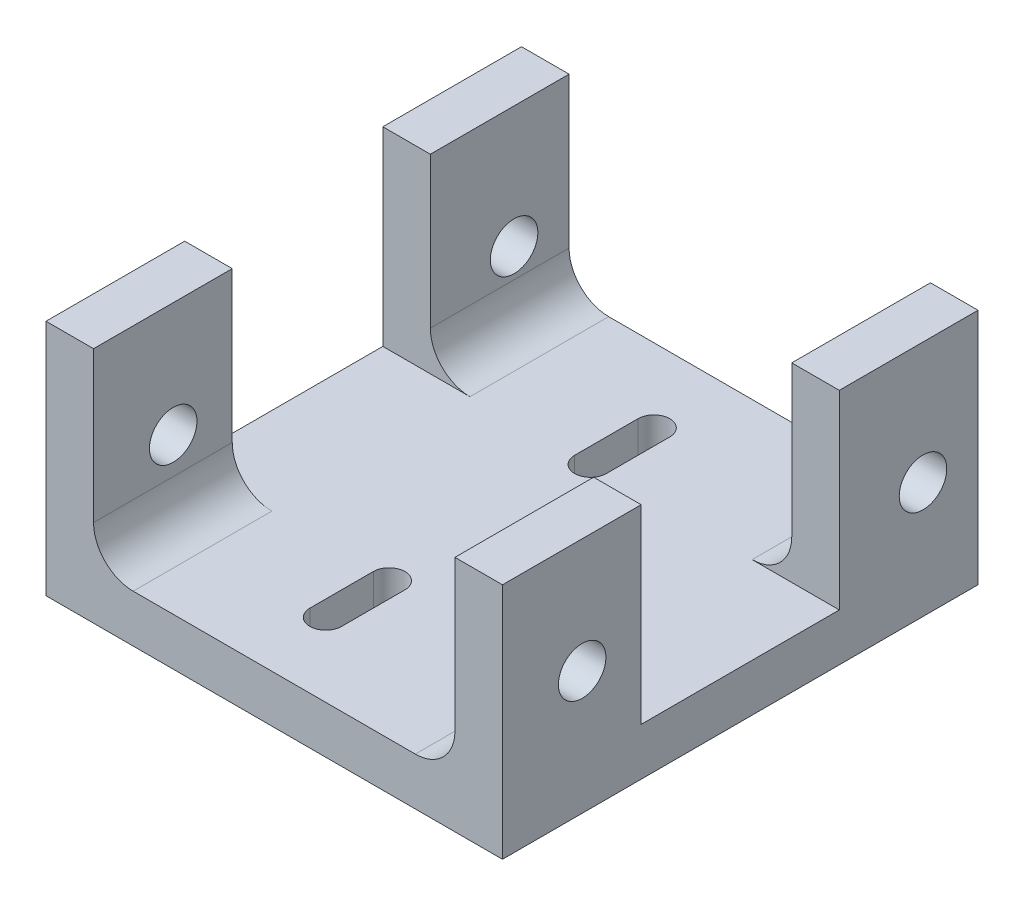
SolidWorks part; units mm, degrees
ref_plane "前视基准面" through (0, 0, 0) normal (0, 0, 1) x (1, 0, 0)
ref_plane "上视基准面" through (0, 0, 0) normal (0, 1, 0) x (1, 0, 0)
ref_plane "右视基准面" through (0, 0, 0) normal (1, 0, 0) x (0, 0, -1)
sketch "草图1" plane through (0, 0, 0) normal (0, 0, 1) x (1, 0, 0)
  line L0 (0, 0) -> (0, 12)
  line L1 (0, 12) -> (-3, 12)
  line L2 (-3, 12) -> (-3, -3)
  line L3 (-3, -3) -> (25.8, -3)
  line L4 (25.8, -3) -> (25.8, 12)
  line L5 (25.8, 12) -> (22.8, 12)
  line L6 (22.8, 12) -> (22.8, 0)
  line L7 (22.8, 0) -> (0, 0)
  dimension "D1" = 3
  dimension "D2" = 3
  dimension "D3" = 28.8
  dimension "D4" = 3
  dimension "D5" = 15
  dimension "D6" = 15
extrude "凸台-拉伸1" add sketch "草图1" along normal blind 30
sketch "草图2" plane through (25.8, 0, 0) normal (1, 0, 0) x (0, 0, -1)
  line L0 (-15, 12) -> (-15, 6) construction
  line L1 (-21.25, 12) -> (-8.75, 12)
  line L2 (-21.25, 12) -> (-21.25, 0)
  line L3 (-21.25, 0) -> (-8.75, 0)
  line L4 (-8.75, 12) -> (-8.75, 0)
  line L5 (-21.25, 12) -> (-8.75, 0) construction
  line L6 (-21.25, 0) -> (-8.75, 12) construction
  line L7 (-30, 12) -> (0, 12) construction
  line L8 (-15, 0) -> (-15, -3) construction
  line L10 (-30, -3) -> (0, -3) construction
  point P0 (-15, 6)
  dimension "D1" = 12.5
  dimension "D2" = 12
  dimension "D3" = 3
extrude "切除-拉伸1" cut sketch "草图2" against normal up to surface (28.8 mm away) up to face at (-3, 4.5, 15)
sketch "草图3" plane through (0, 0, 0) normal (0, 1, 0) x (1, 0, 0)
  line L0 (-3, -15) -> (4, -15) construction
  line L1 (-3, -8.75) -> (-3, -21.25) construction
  line L2 (4, -15) -> (4, -6.5) construction
  line L3 (4, -6.5) -> (10, -6.5) construction
  line L4 (10, -6.5) -> (10, -23.5) construction
  line L5 (10, -23.5) -> (4, -23.5) construction
  line L6 (4, -23.5) -> (4, -15) construction
  line L7 (10, -4.6471) -> (10, -8.6471) construction
  line L8 (11, -4.6471) -> (11, -8.6471)
  line L9 (9, -4.6471) -> (9, -8.6471)
  line L10 (10, -25.3529) -> (10, -21.3529) construction
  line L11 (11, -25.3529) -> (11, -21.3529)
  line L12 (9, -25.3529) -> (9, -21.3529)
  circle A0 centre (10, -6.5) radius 1 construction
  circle A1 centre (10, -23.5) radius 1 construction
  arc A2 (11, -4.6471) -> (9, -4.6471) centre (10, -4.6471) ccw
  arc A3 (9, -8.6471) -> (11, -8.6471) centre (10, -8.6471) ccw
  arc A4 (11, -25.3529) -> (9, -25.3529) centre (10, -25.3529) cw
  arc A5 (9, -21.3529) -> (11, -21.3529) centre (10, -21.3529) cw
  point P12 (10, -6.6471)
  point P19 (10, -23.3529)
  dimension "D5" = 2
  dimension "D6" = 1
  dimension "D1" = 7
  dimension "D2" = 6
  dimension "D3" = 8.5
  dimension "D4" = 8.5
  dimension "D7" = 4
extrude "切除-拉伸2" cut sketch "草图3" against normal up to next
hole_wizard "大小mm Press 暗销孔1" positions "草图4" profile "草图5" hole size "Ø3.0" standard "ISO" end condition through all
sketch "草图4" plane through (-3, 140.1855, 21.2338) normal (-1, 0, 0) x (0, -0.021, -0.9998)
  point P0 (20.6088, 135.4526)
  point P2 (-0.9003, 135.4526)
sketch "草图5" plane through (-3, 4.3306, 3.4697) normal (0, 1, 0) x (0, 0, 1)
  line L0 (0, 0) -> (0, 28.8)
  line L1 (0, 28.8) -> (1.5, 28.8)
  line L2 (1.5, 28.8) -> (1.5, 0)
  line L3 (1.5, 0) -> (0, 0)
  line L4 (0, -6.35) -> (0, 107.95) construction
  dimension "通孔孔直径" = 3
  dimension "通孔孔深度" = 28.8
fillet "圆角1" radius 2.5 4 edges at (22.8, 0, 25.625) (22.8, 0, 4.375) (0, 0, 25.625) (0, 0, 4.375)
